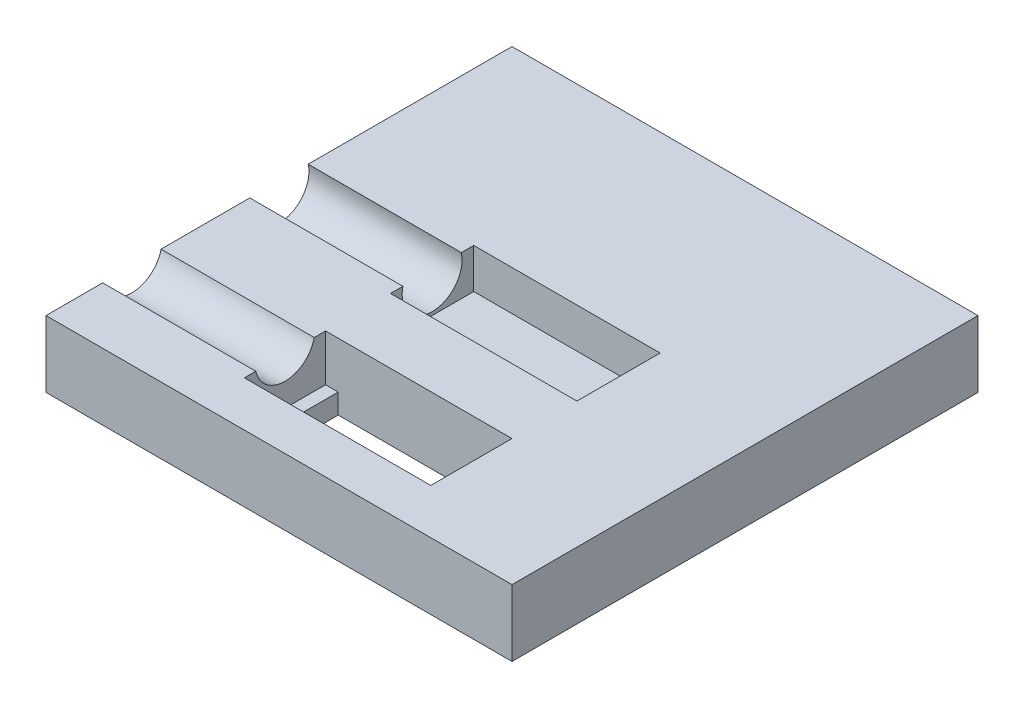
SolidWorks part; units mm, degrees
material "PLA"
ref_plane "Alzado" through (0, 0, 0) normal (0, 0, 1) x (1, 0, 0)
ref_plane "Planta" through (0, 0, 0) normal (0, 1, 0) x (1, 0, 0)
ref_plane "Vista lateral" through (0, 0, 0) normal (1, 0, 0) x (0, 0, -1)
sketch "Croquis1" plane through (0, 0, 0) normal (0, 1, 0) x (1, 0, 0)
  line L1 (-32, 32) -> (32, 32)
  line L2 (-32, 32) -> (-32, -32)
  line L3 (-32, -32) -> (32, -32)
  line L4 (32, 32) -> (32, -32)
  line L5 (-32, 32) -> (32, -32) construction
  line L6 (-32, -32) -> (32, 32) construction
  circle A0 centre (0, 0) radius 31 construction
  point P0 (0, 0)
extrude "Saliente-Extruir1" add sketch "Croquis1" along normal blind 60 contours L1 L4 L3 L2
sketch "Croquis2" plane through (0, 0, 0) normal (0, 1, 0) x (1, 0, 0)
  line L1 (-35, 35) -> (35, 35)
  line L2 (-35, 35) -> (-35, -35)
  line L3 (-35, -35) -> (35, -35)
  line L4 (35, 35) -> (35, -35)
  line L5 (-35, 35) -> (35, -35) construction
  line L6 (-35, -35) -> (35, 35) construction
  line L7 (-32, -32) -> (32, -32)
  line L8 (-32, -32) -> (-32, 32)
  line L9 (-32, 32) -> (32, 32)
  line L10 (32, -32) -> (32, 32)
  line L11 (-32, -32) -> (32, 32) construction
  line L12 (-32, 32) -> (32, -32) construction
  point P0 (0, 0)
  point P6 (0, 0)
extrude "Saliente-Extruir2" add sketch "Croquis2" along normal blind 64
sketch "Croquis3" plane through (0, 64, 0) normal (0, 1, 0) x (1, 0, 0)
  line L0 (0, 0) -> (16, 0) construction
  line L1 (0, 0) -> (0, 3.6) construction
  line L2 (0, 1.8) -> (1.9, 1.8) construction
  line L3 (1.9, 0) -> (1.9, 1.8) construction
  line L4 (1.9, 1.8) -> (1.9, 3.0578) construction
  line L5 (16, -2) -> (16, 2)
  line L6 (1.9, 3.0578) -> (16, 2)
  line L7 (1.9, -3.0578) -> (16, -2)
  line L8 (-1.9, -3.0578) -> (-16, -2)
  line L9 (-16, -2) -> (-16, 2)
  line L10 (-1.9, 3.0578) -> (-16, 2)
  circle A0 centre (0, 0) radius 3.6 construction
  arc A1 (-1.9, 3.0578) -> (1.9, 3.0578) centre (0, 0) cw
  arc A2 (-1.9, -3.0578) -> (1.9, -3.0578) centre (0, 0) ccw
sketch "Croquis4" plane through (0, 60, 0) normal (0, 1, 0) x (1, 0, 0)
  line L0 (0, 0) -> (-7, 0) construction
  line L1 (-7, 6) -> (-7, -6)
  line L3 (16, -6) -> (16, 6)
  line L5 (-7, 6) -> (-7, 6.25)
  line L6 (16, -6) -> (16, -6.25)
  line L7 (16, -6.25) -> (-7, -6.25)
  line L8 (-7, -6.25) -> (-7, -6)
  line L9 (-7, 6.25) -> (16, 6.25)
  line L10 (16, 6.25) -> (16, 6)
  point P8 (16, 0)
extrude "Cortar-Extruir1" cut sketch "Croquis4" against normal blind 21
sketch "Croquis5" plane through (0, 60, 0) normal (0, 1, 0) x (1, 0, 0)
  line L0 (16, 0) -> (19, 0) construction
  line L1 (-7, 0) -> (-9, 0) construction
  line L2 (-7, 6.25) -> (-7, -6.25) construction
  circle A0 centre (19, 0) radius 1.1
  circle A1 centre (-9, 0) radius 1.1
extrude "Cortar-Extruir2" cut sketch "Croquis5" against normal blind 10
sketch "Croquis10" plane through (-7, 0, 0) normal (1, 0, 0) x (0, 0, -1)
  line L0 (0, 39) -> (0, 44)
  line L2 (0, 39) -> (0, 60) construction
  line L3 (6.25, 39) -> (-6.25, 39) construction
  line L4 (6.25, 60) -> (-6.25, 60) construction
  circle A0 centre (0, 44) radius 4.5
extrude "Cortar-Extruir3" cut sketch "Croquis10" against normal up to next contours L2 L0 A0 | L0 L2 A0
sketch "Croquis11" plane through (0, 0, 0) normal (0, -1, 0) x (1, 0, 0)
  line L1 (-35, 35) -> (35, 35)
  line L2 (-35, 35) -> (-35, -35)
  line L3 (-35, -35) -> (35, -35)
  line L4 (35, 35) -> (35, -35)
  line L5 (-35, 35) -> (35, -35) construction
  line L6 (-35, -35) -> (35, 35) construction
  point P0 (0, 0)
extrude "Cortar-Extruir4" cut sketch "Croquis11" against normal blind 30
sketch "Croquis12" plane through (0, 30, 0) normal (0, -1, 0) x (1, 0, 0)
  line L0 (0, 0) -> (0, 22.1) construction
  line L1 (0, 22.1) -> (16, 22.1) construction
  line L2 (16, 20.2) -> (16, 24) construction
  line L3 (1.9, 0) -> (1.9, 22.1) construction
  line L4 (1.9, 22.1) -> (1.9, 25.0578) construction
  line L5 (1.9, 25.0578) -> (16, 24) construction
  line L6 (1.9, 19.1422) -> (16, 20.2) construction
  line L7 (-1.9, 25.0578) -> (-16, 24) construction
  line L8 (-16, 20.2) -> (-16, 24) construction
  line L9 (-1.9, 19.1422) -> (-16, 20.2) construction
  line L10 (0, 22.1) -> (-7, 22.1) construction
  line L11 (-7, 28.2) -> (-7, 16)
  line L12 (-7, 16) -> (16, 16)
  line L13 (16, 16) -> (16, 28.2)
  line L14 (-7, 28.2) -> (16, 28.2)
  line L15 (0, 0) -> (19.54, 0) construction
  circle A0 centre (0, 22.1) radius 3.5155 construction
  arc A1 (1.9, 25.0578) -> (-1.9, 25.0578) centre (0, 22.1) ccw construction
  arc A2 (1.9, 19.1422) -> (-1.9, 19.1422) centre (0, 22.1) cw construction
  circle A3 centre (0, 22.1) radius 24 construction
  circle A4 centre (0, -22.1) radius 24 construction
extrude "Cortar-Extruir5" cut sketch "Croquis12" against normal blind 21
sketch "Croquis13" plane through (-7, 0, 0) normal (1, 0, 0) x (0, 0, -1)
  line L0 (-22.1, 30) -> (-22.1, 46) construction
  line L2 (-28.2, 30) -> (-16, 30) construction
  circle A0 centre (-22.1, 46) radius 4.5
extrude "Cortar-Extruir6" cut sketch "Croquis13" against normal up to next
sketch "Croquis14" plane through (0, 30, 0) normal (0, -1, 0) x (1, 0, 0)
  line L0 (16, 22.1) -> (19, 22.1) construction
  line L1 (-7, 22.1) -> (-9, 22.1) construction
  circle A0 centre (19, 22.1) radius 1.1
  circle A1 centre (-9, 22.1) radius 1.1
extrude "Cortar-Extruir7" cut sketch "Croquis14" against normal blind 10
sketch "Croquis15" plane through (0, 30, 0) normal (0, -1, 0) x (1, 0, 0)
  circle A0 centre (0, -22.1) radius 3.7
extrude "Cortar-Extruir8" cut sketch "Croquis15" against normal blind 10 contours A0
sketch "Croquis16" plane through (0, 60, 0) normal (0, 1, 0) x (1, 0, 0)
  line L1 (-32, -32) -> (32, -32)
  line L2 (-32, -32) -> (-32, 32)
  line L3 (-32, 32) -> (32, 32)
  line L4 (32, -32) -> (32, 32)
  line L5 (-32, -32) -> (32, 32) construction
  line L6 (-32, 32) -> (32, -32) construction
  point P0 (0, 0)
extrude "Cortar-Extruir9" cut sketch "Croquis16" against normal blind 5
sketch "Croquis17" plane through (-7, 0, 0) normal (1, 0, 0) x (0, 0, -1)
  line L0 (6.25, 55) -> (6.25, 51.9987) construction
  line L1 (6.25, 39) -> (6.25, 55) construction
  line L2 (6.25, 51.9987) -> (-6.25, 51.9987)
  line L3 (-6.25, 39) -> (-6.25, 55) construction
  line L4 (-6.25, 51.9987) -> (-6.25, 39)
  line L5 (-6.25, 39) -> (6.25, 39)
  line L6 (6.25, 39) -> (-6.25, 39) construction
  line L7 (6.25, 39) -> (6.25, 51.9987)
extrude "Cortar-Extruir10" cut sketch "Croquis17" against normal blind 5
sketch "Croquis18" plane through (35, 0, 0) normal (1, 0, 0) x (0, 0, -1)
  line L0 (35, 64) -> (35, 30) construction
  line L1 (-35, 64) -> (35, 64)
  line L2 (-35, 64) -> (-35, 55)
  line L3 (-35, 55) -> (35, 55)
  line L4 (35, 64) -> (35, 55)
  line L5 (-35, 30) -> (-35, 35.0002)
  line L6 (-35, 64) -> (-35, 30) construction
  line L7 (-35, 35.0002) -> (35, 35.0002)
  line L8 (35, 35.0002) -> (35, 30)
  line L9 (-1.9, 30) -> (46.1, 30) construction
  line L10 (35, 30) -> (-35, 30)
extrude "Cortar-Extruir11" cut sketch "Croquis18" against normal up to next
sketch "Croquis19" plane through (-7, 0, 0) normal (1, 0, 0) x (0, 0, -1)
  line L0 (-16, 30) -> (-16, 33) construction
  line L1 (-16, 51) -> (-16, 35.0002) construction
  line L2 (-16, 51) -> (-28.2, 51)
  line L7 (-22.1, 35.0002) -> (-22.1, 38.0002) construction
  line L8 (-16, 35.0002) -> (-28.2, 35.0002) construction
  line L9 (-22.1, 38.0002) -> (-16, 38.0002)
  line L10 (-22.1, 38.0002) -> (-28.2, 38.0002)
  line L11 (-28.2, 51) -> (-28.2, 38.0002)
  line L12 (-16, 51) -> (-16, 38.0002)
  line L13 (-22.1, 35.0002) -> (-16, 35.0002) construction
  line L14 (-16, 35.0002) -> (-16, 33) construction
extrude "Cortar-Extruir13" cut sketch "Croquis19" against normal blind 5
ref_plane "Plano1" through (0, 45.0002, 0) normal (0, -1, 0) x (-1, 0, 0)
sketch "Croquis21" plane through (0, 45.0002, 0) normal (0, -1, 0) x (-1, 0, 0)
  line L1 (-40.6571, 39.9693) -> (40.8099, 39.9693)
  line L2 (-40.6571, 39.9693) -> (-40.6571, -41.4977)
  line L3 (-40.6571, -41.4977) -> (40.8099, -41.4977)
  line L4 (40.8099, 39.9693) -> (40.8099, -41.4977)
extrude "Cortar-Extruir14" cut sketch "Croquis21" against normal up to next
sketch "Croquis22" plane through (0, 38.0002, 0) normal (0, 1, 0) x (1, 0, 0)
  line L1 (-7, -16) -> (-10.1, -16)
  line L2 (-7, -16) -> (-7, -28.2)
  line L3 (-7, -28.2) -> (-10.1, -28.2)
  line L4 (-10.1, -16) -> (-10.1, -28.2)
extrude "Cortar-Extruir15" cut sketch "Croquis22" against normal up to next
